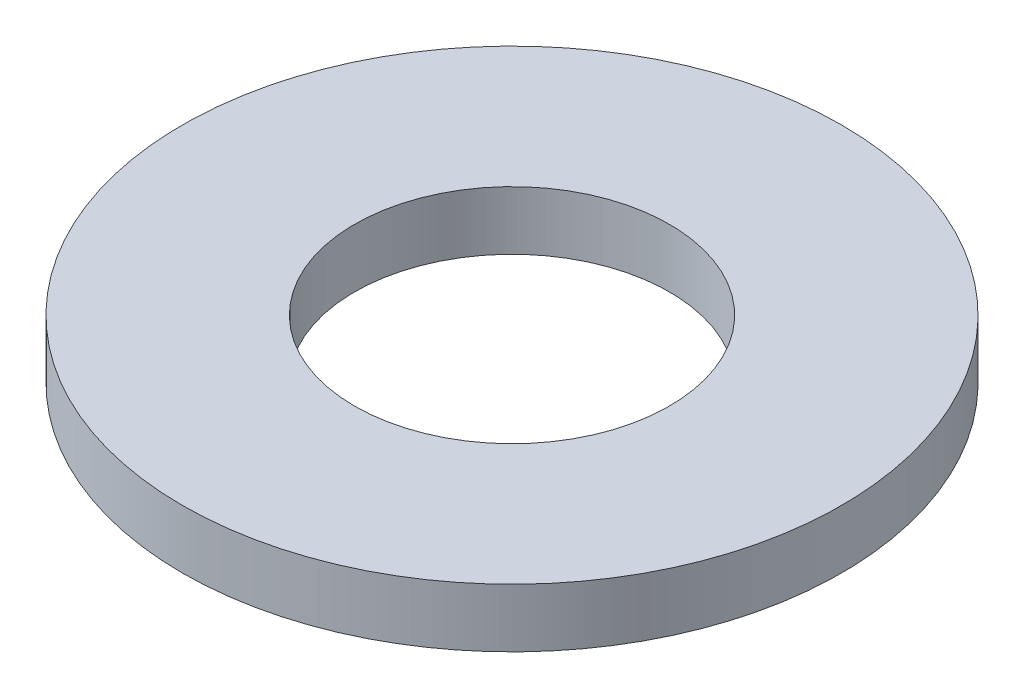
SolidWorks part; units mm, degrees
material "1060 Alloy"
ref_plane "Front Plane" through (0, 0, 0) normal (0, 0, 1) x (1, 0, 0)
ref_plane "Top Plane" through (0, 0, 0) normal (0, 1, 0) x (1, 0, 0)
ref_plane "Right Plane" through (0, 0, 0) normal (1, 0, 0) x (0, 0, -1)
sketch "Sketch1" plane through (0, 0, 0) normal (0, 1, 0) x (1, 0, 0)
  circle A0 centre (0, 0) radius 2.15
  circle A1 centre (0, 0) radius 4.5
  dimension "D1" = 4.3
  dimension "D2" = 9
extrude "Boss-Extrude1" add sketch "Sketch1" along normal blind 0.8
